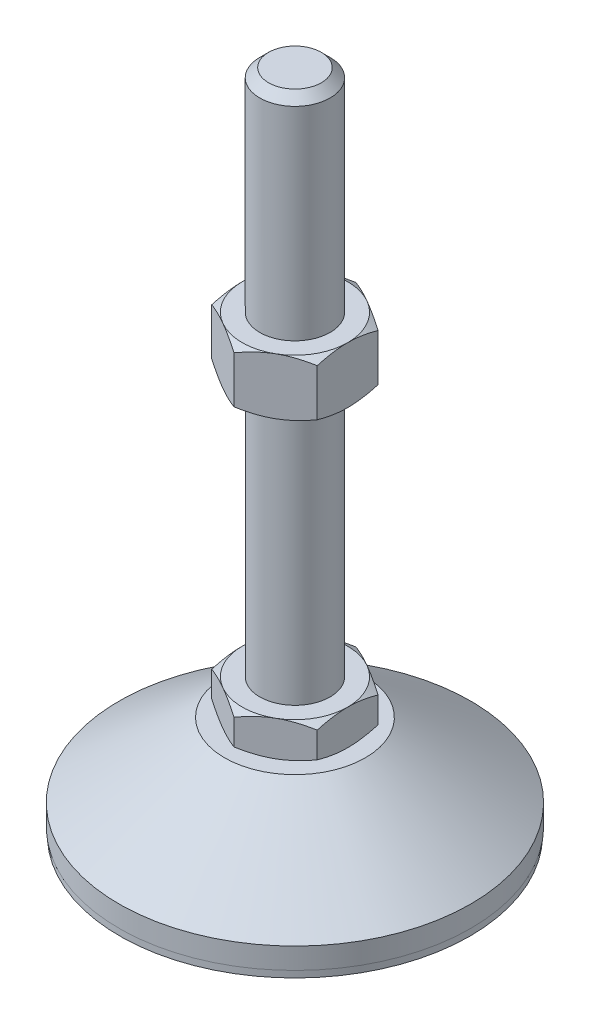
SolidWorks part; units mm, degrees
ref_plane "Спереди" through (0, 0, 0) normal (0, 0, 1) x (1, 0, 0)
ref_plane "Сверху" through (0, 0, 0) normal (0, 1, 0) x (1, 0, 0)
ref_plane "Справа" through (0, 0, 0) normal (1, 0, 0) x (0, 0, -1)
sketch "Эскиз1" plane through (0, 0, 0) normal (0, 0, 1) x (1, 0, 0)
  line L0 (0, 0) -> (-49.8, 0)
  line L1 (-49.8, 0) -> (-49.8, 2)
  line L2 (-49.8, 2) -> (-50, 2)
  line L3 (-50, 2) -> (-50, 8)
  line L4 (-50, 8) -> (-20, 29)
  line L5 (-20, 29) -> (-10, 29)
  line L12 (-10, 39) -> (-10, 186.5)
  line L13 (-10, 186.5) -> (-7.5, 189)
  line L14 (-7.5, 189) -> (0, 189)
  line L15 (0, 189) -> (0, 0) construction
  line L16 (-10, 29) -> (0, 29) construction
  line L17 (0, 0) -> (0, 189)
  line L18 (0, 0) -> (0, -7.9595) construction
  line L19 (-10, 39) -> (-10, 29)
  point P8 (-10, 112.75)
  point P23 (-15, 29)
  dimension "D1" = 20
  dimension "D2" = 29
  dimension "D3" = 10
  dimension "D4" = 100
  dimension "D5" = 10
  dimension "D6" = 2.5
  dimension "D7" = 45
  dimension "D8" = 40
  dimension "D9" = 2
  dimension "D10" = 150
  dimension "D11" = 6
  dimension "D12" = 0.2
revolve "Повернуть1" add sketch "Эскиз1" angle 360 about L17
sketch "Эскиз2" plane through (0, 29, 0) normal (0, 1, 0) x (1, 0, 0)
  line L1 (0, 17.3205) -> (-15, 8.6603)
  line L2 (-15, 8.6603) -> (-15, -8.6603)
  line L3 (-15, -8.6603) -> (0, -17.3205)
  line L4 (0, -17.3205) -> (15, -8.6603)
  line L5 (15, -8.6603) -> (15, 8.6603)
  line L6 (15, 8.6603) -> (0, 17.3205)
  circle A0 centre (0, 0) radius 15 construction
  dimension "D1" = 30
extrude "Бобышка-Вытянуть1" add sketch "Эскиз2" along normal up to vertex (10 mm away) up to point (-10, 39, 0)
ref_plane "Плоскость1" through (0, 112.75, 0) normal (0, 1, 0) x (1, 0, 0)
sketch "Эскиз3" plane through (0, 112.75, 0) normal (0, 1, 0) x (1, 0, 0)
  line L6 (15, 8.6603) -> (0, 17.3205)
  line L7 (0, 17.3205) -> (-15, 8.6603)
  line L8 (-15, 8.6603) -> (-15, -8.6603)
  line L9 (-15, -8.6603) -> (0, -17.3205)
  line L10 (0, -17.3205) -> (15, -8.6603)
  line L11 (15, -8.6603) -> (15, 8.6603)
  line L12 (15, 8.6603) -> (0, 17.3205)
  line L13 (0, 17.3205) -> (-15, 8.6603)
  line L14 (-15, 8.6603) -> (-15, -8.6603)
  line L15 (-15, -8.6603) -> (0, -17.3205)
  line L16 (0, -17.3205) -> (15, -8.6603)
  line L17 (15, -8.6603) -> (15, 8.6603)
  dimension "D1" = 0
extrude "Бобышка-Вытянуть2" add sketch "Эскиз3" along normal blind 16
sketch "Эскиз4" plane through (0, 0, 0) normal (0, 0, 1) x (1, 0, 0)
  line L0 (-15, 128.75) -> (-28.8564, 120.75)
  line L1 (-28.8564, 120.75) -> (-28.8564, 128.75)
  line L2 (-28.8564, 128.75) -> (-15, 128.75)
  line L3 (-28.8564, 120.75) -> (-15, 112.75)
  line L4 (50, 112.75) -> (-50, 112.75) construction
  line L5 (-15, 112.75) -> (-28.8564, 112.75)
  line L6 (-28.8564, 112.75) -> (-28.8564, 120.75)
  line L7 (-15, 128.75) -> (-15, 112.75) construction
  line L8 (-15, 39) -> (-23.6603, 39)
  line L9 (-23.6603, 39) -> (-23.6603, 34)
  line L10 (-23.6603, 34) -> (-15, 39)
  line L11 (-15, 29) -> (-23.6603, 34)
  line L12 (-23.6603, 34) -> (-23.6603, 29)
  line L13 (-23.6603, 29) -> (-15, 29)
  line L14 (0, 189) -> (0, 96.3793) construction
  dimension "D1" = 30
  dimension "D2" = 30
revolve "Вырез-Повернуть2" cut sketch "Эскиз4" angle 360 about L14
